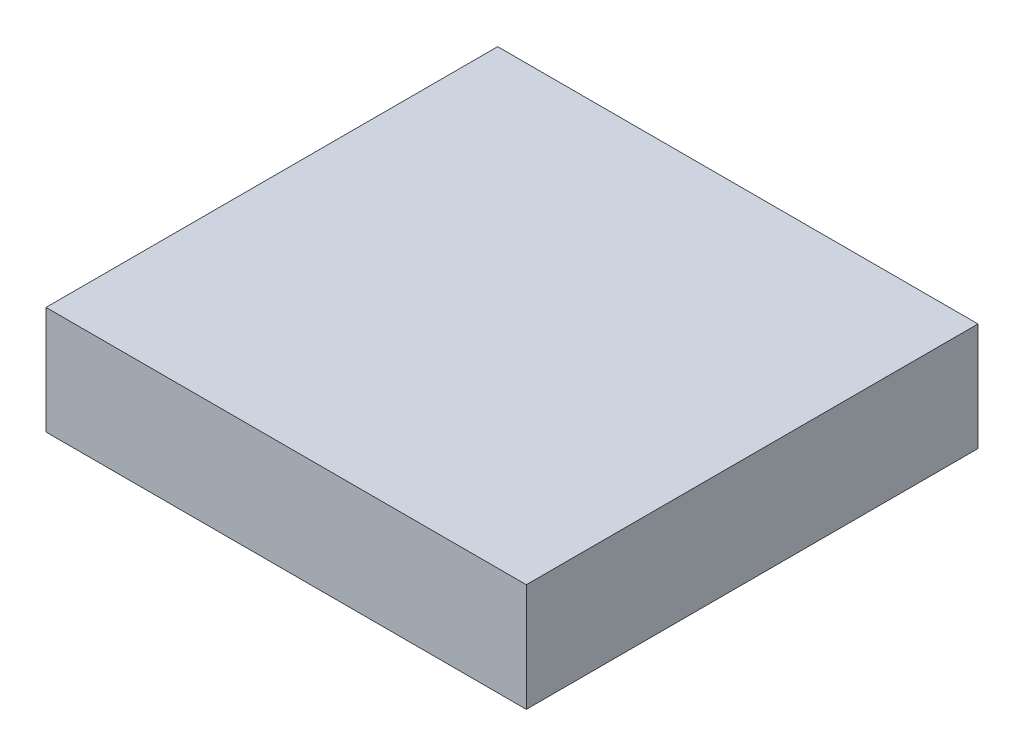
SolidWorks part; units mm, degrees
ref_plane "Front Plane" through (0, 0, 0) normal (0, 0, 1) x (1, 0, 0)
ref_plane "Top Plane" through (0, 0, 0) normal (0, 1, 0) x (1, 0, 0)
ref_plane "Right Plane" through (0, 0, 0) normal (1, 0, 0) x (0, 0, -1)
sketch "Sketch1" plane through (0, 0, 0) normal (0, 1, 0) x (1, 0, 0)
  line L1 (-47.895, 45.085) -> (47.995, 45.085)
  line L2 (-47.895, 45.085) -> (-47.895, -45.085)
  line L3 (-47.895, -45.085) -> (47.995, -45.085)
  line L4 (47.995, 45.085) -> (47.995, -45.085)
  dimension "D1" = 95.89
  dimension "D2" = 90.17
  dimension "D3" = 45.085
  dimension "D4" = 47.895
extrude "Boss-Extrude1" add sketch "Sketch1" along normal mid plane 21.55
